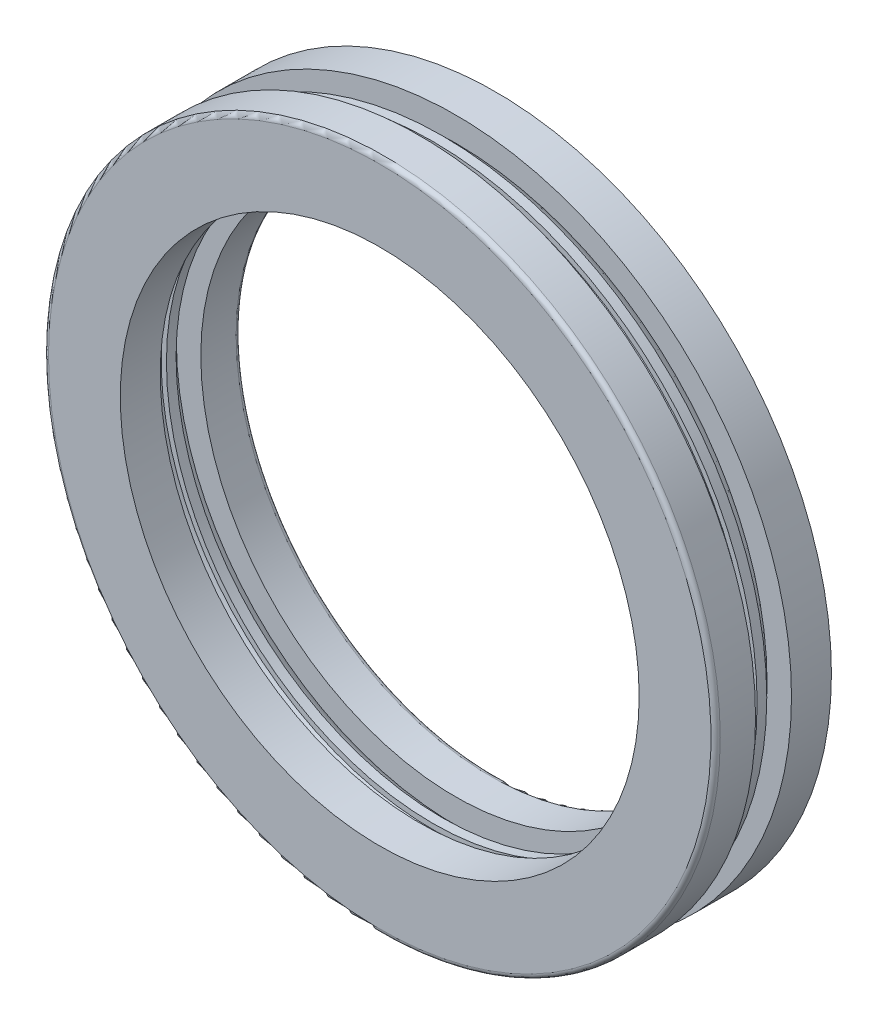
SolidWorks part; units mm, degrees
ref_plane "Front Plane" through (0, 0, 0) normal (0, 0, 1) x (1, 0, 0)
ref_plane "Top Plane" through (0, 0, 0) normal (0, 1, 0) x (1, 0, 0)
ref_plane "Right Plane" through (0, 0, 0) normal (1, 0, 0) x (0, 0, -1)
sketch "BaseSke" plane through (0, 0, 0) normal (1, 0, 0) x (0, 0, -1)
  line L0 (-22.7078, 0) -> (24.6132, 0) construction
  line L1 (-22.7078, 63.75) -> (24.6132, 63.75) construction
  line L2 (0, 129.5214) -> (0, -86.3012) construction
  line L3 (0, 68.9583) -> (0, 58.5417)
  line L6 (-12.5, 72.5) -> (-12.5, 56) construction
  line L8 (12.5, 72.5) -> (12.5, 55) construction
  arc A0 (0, 68.9583) -> (0, 58.5417) centre (0, 63.75) ccw
  dimension "Ball_diameter" = 10.4167
  dimension "Diameter2" = 145
  dimension "Bearing_Inside_Diameter" = 110
  dimension "D1" = 63.75
  dimension "D2" = 12.5
  dimension "Bearing_Thickness" = 25
  dimension "Diameter1" = 112
  dimension "Bearing_Outside_Diameter" = 145
revolve "Ball" add sketch "BaseSke" angle 360 about L3
sketch "InnerRaceSke" plane through (0, 0, 0) normal (1, 0, 0) x (0, 0, -1)
  line L0 (3.8793, 60.2897) -> (3.8793, 55)
  line L1 (3.8793, 72.5) -> (12.5, 72.5)
  line L2 (3.8793, 72.5) -> (3.8793, 67.2103)
  line L3 (3.8793, 55) -> (12.5, 55)
  line L4 (12.5, 72.5) -> (12.5, 55)
  line L5 (-18.959, 0) -> (19.5136, 0) construction
  arc A0 (3.8793, 60.2897) -> (3.8793, 67.2103) centre (0, 63.75) ccw
  arc A2 (0, 68.9583) -> (0, 58.5417) centre (0, 63.75) ccw construction
  dimension "D1" = 10.3967
  dimension "D2" = 8.6207
revolve "InnerRace" add sketch "InnerRaceSke" angle 360 about L5
sketch "OuterRaceSke" plane through (0, 0, 0) normal (1, 0, 0) x (0, 0, -1)
  line L0 (-3.8793, 60.2897) -> (-3.8793, 56)
  line L1 (-12.5, 72.5) -> (-3.8793, 72.5)
  line L2 (-12.5, 72.5) -> (-12.5, 56)
  line L3 (-12.5, 56) -> (-3.8793, 56)
  line L4 (-3.8793, 72.5) -> (-3.8793, 67.2103)
  line L5 (-27.1643, 0) -> (37.3715, 0) construction
  arc A0 (-3.8793, 67.2103) -> (-3.8793, 60.2897) centre (0, 63.75) ccw
  arc A1 (0, 68.9583) -> (0, 58.5417) centre (0, 63.75) ccw construction
  dimension "D1" = 10.3967
  dimension "D2" = 8.6207
revolve "OuterRace" add sketch "OuterRaceSke" angle 360 about L5
fillet "Fillet1" radius 1 2 edges at (72.5, 0, 12.5) (55, 0, -12.5)
pattern_circular "CirPatternBall" [suppressed] count 26 over 360 about axis through (0, 0, 27.1643) along (0, 0, -1)
sketch "CageSke" plane through (0, 0, 0) normal (1, 0, 0) x (0, 0, -1)
  line L0 (0, 59.1614) -> (0, 0) construction
  line L1 (1.0417, 70) -> (-1.0417, 70)
  line L2 (1.0417, 70) -> (1.0417, 57.5)
  line L3 (1.0417, 57.5) -> (-1.0417, 57.5)
  line L4 (-1.0417, 70) -> (-1.0417, 57.5)
  line L5 (-23.077, 0) -> (28.998, 0) construction
  circle A0 centre (0, 63.75) radius 6.3362 construction
  arc A1 (0, 68.9583) -> (0, 58.5417) centre (0, 63.75) ccw construction
  dimension "D1" = 2.0833
  dimension "D2" = 12.5
revolve "Cage" add sketch "CageSke" angle 360 about L5
sketch "SimplifiedSke" plane through (0, 0, 0) normal (1, 0, 0) x (0, 0, -1)
  line L0 (-32.3536, 0) -> (41.9236, 0) construction
  circle A0 centre (0, 63.75) radius 5.2083
  arc A1 (0, 68.9583) -> (0, 58.5417) centre (0, 63.75) ccw construction
revolve "Simplified" add sketch "SimplifiedSke" angle 360 about L0
equation "\"D2@BaseSke\" = \"Bearing_Thickness@BaseSke\"/2"
equation "\"D1@BaseSke\" =  ( \"Diameter2@BaseSke\" + \"Bearing_Inside_Diameter@BaseSke\" )  / 4"
equation "\"Ball_diameter@BaseSke\" = \"Bearing_Thickness@BaseSke\"  / 2.4"
equation "\"D1@InnerRaceSke\" = \"Ball_diameter@BaseSke\"-0.02"
equation "\"D2@InnerRaceSke\" = \"Bearing_Thickness@BaseSke\"/2.9"
equation "\"D1@OuterRaceSke\" = \"Ball_diameter@BaseSke\"-0.02"
equation "\"D2@OuterRaceSke\" = \"Bearing_Thickness@BaseSke\" / 2.9"
equation "\"D1@CirPatternBall\" =  pi  * \"D1@BaseSke\" * 2 / \"Ball_diameter@BaseSke\"/1.5"
equation "\"D1@CageSke\" = \"Ball_diameter@BaseSke\"/5"
equation "\"D2@CageSke\" = \"Ball_diameter@BaseSke\" * 1.2"
